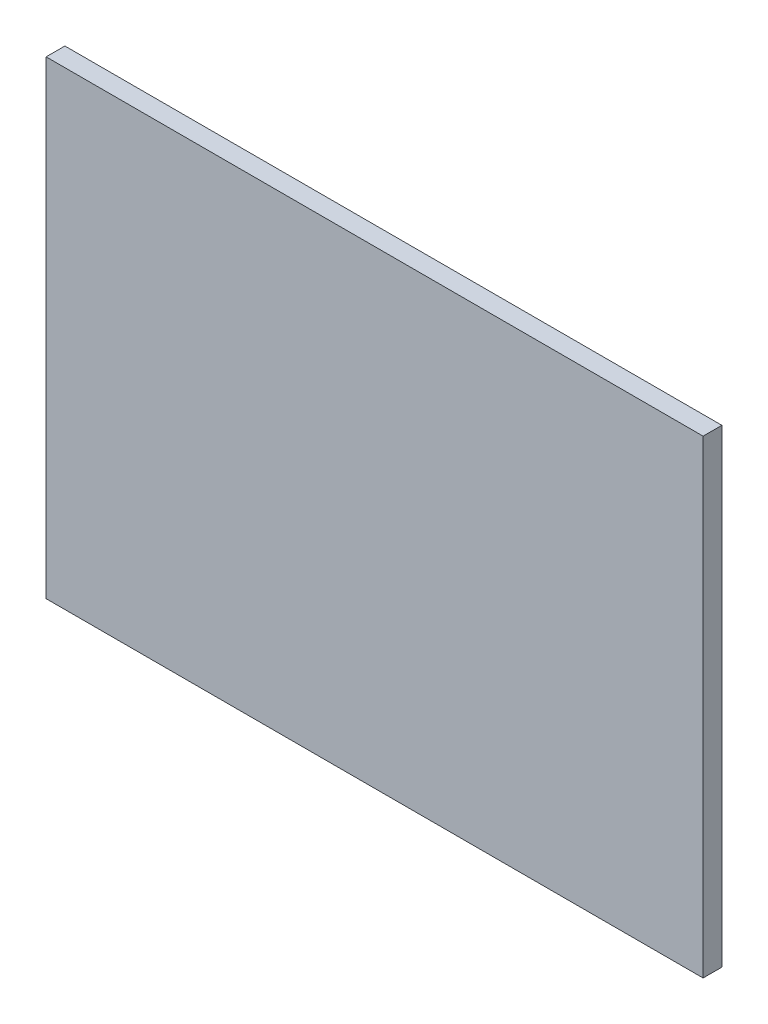
SolidWorks part; units mm, degrees
ref_plane "Ebene vorne" through (0, 0, 0) normal (0, 0, 1) x (1, 0, 0)
ref_plane "Ebene oben" through (0, 0, 0) normal (0, 1, 0) x (1, 0, 0)
ref_plane "Ebene rechts" through (0, 0, 0) normal (1, 0, 0) x (0, 0, -1)
sketch "Skizze1" plane through (0, 0, 0) normal (0, 0, 1) x (1, 0, 0)
  line L1 (0, 0) -> (70, 0)
  line L2 (0, 0) -> (0, 50)
  line L3 (0, 50) -> (70, 50)
  line L4 (70, 0) -> (70, 50)
  dimension "D1" = 70
  dimension "D2" = 50
extrude "Aufsatz-Linear austragen1" add sketch "Skizze1" along normal blind 2
